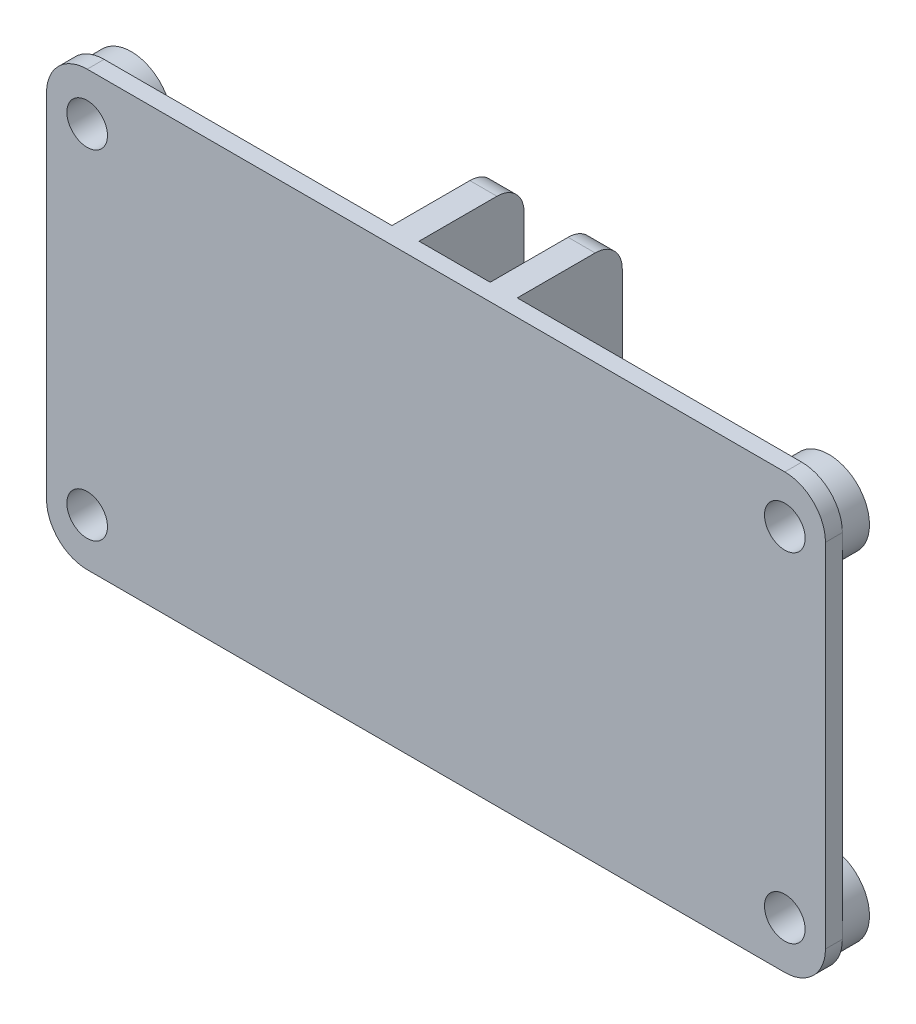
SolidWorks part; units mm, degrees
ref_plane "Plan de face" through (0, 0, 0) normal (0, 0, 1) x (1, 0, 0)
ref_plane "Plan de dessus" through (0, 0, 0) normal (0, 1, 0) x (1, 0, 0)
ref_plane "Plan de droite" through (0, 0, 0) normal (1, 0, 0) x (0, 0, -1)
sketch "Esquisse1" plane through (0, 0, 0) normal (0, 0, 1) x (1, 0, 0)
  line L1 (0, 0) -> (57.5, 0)
  line L2 (0, 0) -> (0, 32)
  line L3 (0, 32) -> (57.5, 32)
  line L4 (57.5, 0) -> (57.5, 32)
  point P4 (0, 0)
  point P5 (0, 0)
  point P6 (0, 0)
  point P7 (0, 0)
  point P8 (0, 0)
  point P9 (0, 0)
  point P10 (0, 0)
extrude "Boss.-Extru.1" add sketch "Esquisse1" along normal blind 9
sketch "Esquisse2" plane through (0, 0, 0) normal (0, 0, -1) x (-1, 0, 0)
  line L1 (-24.25, 32) -> (0, 32)
  line L2 (-24.25, 32) -> (-24.25, 0)
  line L3 (-24.25, 0) -> (0, 0)
  line L4 (0, 32) -> (0, 0)
  line L5 (-57.5, 32) -> (-33.5, 32)
  line L6 (-57.5, 32) -> (-57.5, 0)
  line L7 (-57.5, 0) -> (-33.5, 0)
  line L8 (-33.5, 32) -> (-33.5, 0)
  line L9 (-26.25, 32) -> (-31.5, 32)
  line L10 (-26.25, 32) -> (-26.25, 0)
  line L11 (-26.25, 0) -> (-31.5, 0)
  line L12 (-31.5, 32) -> (-31.5, 0)
  point P12 (0, 0)
  point P13 (0, 0)
  point P14 (0, 0)
  point P15 (0, 0)
  point P16 (0, 0)
  point P17 (0, 0)
  point P18 (0, 0)
  point P19 (0, 0)
  point P20 (0, 0)
  point P21 (0, 0)
extrude "Enlèv. mat.-Extru.1" cut sketch "Esquisse2" against normal blind 7.75
sketch "Esquisse3" plane through (33.5, 0, 0) normal (1, 0, 0) x (0, 0, -1)
  circle A0 centre (-3.5, 10) radius 1.55
  circle A2 centre (-3.5, 20) radius 1.55
  point P2 (0, 0)
  point P7 (-3.9715, 21.963)
  point P8 (0, 0)
  point P9 (0, 0)
  point P10 (0, 0)
  point P11 (0, 0)
  point P12 (0, 0)
  point P13 (0, 0)
  point P14 (-4.8073, 26.3238)
extrude "Enlèv. mat.-Extru.2" cut sketch "Esquisse3" against normal through all
fillet "Congé1" radius 3 4 edges at (0, 0, 8.375) (57.5, 0, 8.375) (0, 32, 8.375) (57.5, 32, 8.375)
fillet "Congé2" radius 2 4 edges at (25.25, 0, 0) (32.5, 0, 0) (25.25, 32, 0) (32.5, 32, 0)
sketch "Esquisse10" plane through (0, 0, 7.75) normal (0, 0, -1) x (-1, 0, 0)
  circle A0 centre (-54.5, 28.5) radius 3
  circle A1 centre (-54.5, 3.5) radius 3
  circle A2 centre (-3, 3.5) radius 3
  circle A3 centre (-3, 28.5) radius 3
extrude "Boss.-Extru.2" add sketch "Esquisse10" along normal blind 2
sketch "Esquisse9" plane through (0, 0, 7.75) normal (0, 0, -1) x (-1, 0, 0)
  circle A1 centre (-54.5, 28.5) radius 1.5
  circle A2 centre (-3, 28.5) radius 1.5
  circle A3 centre (-3, 3.5) radius 1.5
  circle A4 centre (-54.5, 3.5) radius 1.5
  point P8 (0, 0)
  point P9 (0, 0)
  point P10 (0, 0)
  point P11 (0, 0)
  point P12 (0, 0)
  point P13 (0, 0)
  point P14 (0, 0)
  point P15 (0, 0)
  point P16 (0, 0)
  point P17 (0, 0)
  point P18 (0, 0)
  point P19 (0, 0)
  point P20 (0, 0)
  point P21 (0, 0)
  point P22 (0, 0)
  point P23 (0, 0)
  point P24 (0, 0)
  point P25 (0, 0)
  point P26 (0, 0)
  point P27 (0, 0)
  point P28 (0, 0)
  point P29 (0, 0)
  point P30 (0, 0)
extrude "Enlèv. mat.-Extru.3" cut sketch "Esquisse9" against normal through all both and the other way through all
